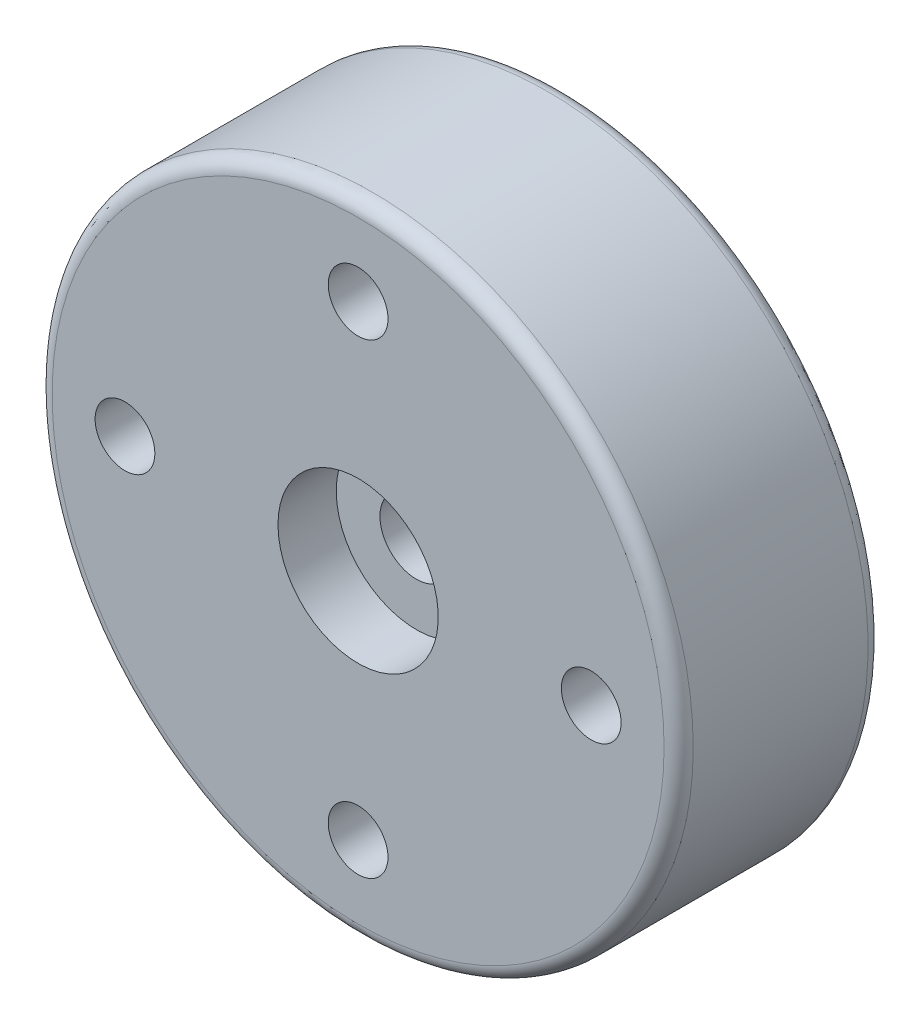
SolidWorks part; units mm, degrees
ref_plane "Front" through (0, 0, 0) normal (0, 0, 1) x (1, 0, 0)
ref_plane "Top" through (0, 0, 0) normal (0, 1, 0) x (1, 0, 0)
ref_plane "Right" through (0, 0, 0) normal (1, 0, 0) x (0, 0, -1)
sketch "Sketch1" plane through (0, 0, 0) normal (1, 0, 0) x (0, 0, -1)
  line L0 (0, 0) -> (-91.1734, 0) construction
  line L1 (3.5, 1.25) -> (2, 1.25)
  line L2 (0, 2.75) -> (0, 11)
  line L3 (0, 11) -> (7, 11)
  line L4 (7, 11) -> (7, 2.75)
  line L5 (7, 2.75) -> (3.5, 2.75)
  line L8 (3.5, 2.75) -> (3.5, 1.25)
  line L9 (0, 2.75) -> (2, 2.75)
  line L10 (2, 2.75) -> (2, 1.25)
  dimension "D1" = 2.5
  dimension "D2" = 5.5
  dimension "D3" = 2
  dimension "D4" = 7
  dimension "D5" = 22
  dimension "D6" = 1.5
revolve "Revolve1" add sketch "Sketch1" angle 360 about L0
hole_wizard "M2 Tapped Hole1" positions "Sketch3" profile "Sketch4" tap size "M2" standard "ISO" end condition up to next
sketch "Sketch3" plane through (0, 0, 0) normal (0, 0, 1) x (1, 0, 0)
  circle A0 centre (0, 0) radius 8 construction
  point P0 (0, 8)
  point P14 (8, 0)
  point P15 (0, -8)
  point P16 (-8, 0)
  point P17 (0, 0)
  dimension "D1" = 16
  dimension "D2" = 4
sketch "Sketch4" plane through (0, 8, 0) normal (1, 0, 0) x (0, -1, 0)
  line L0 (0, 0) -> (0, 7)
  line L1 (0, 7) -> (1.025, 7)
  line L2 (0.8, 6.8701) -> (0.8, 0.1299)
  line L3 (0.8, 0.1299) -> (1.025, 0)
  line L5 (1.025, 0) -> (0, 0)
  line L6 (-0.8, 0.1299) -> (-1.025, 0) construction
  line L7 (1.025, 7) -> (0.8, 6.8701)
  line L8 (-1.025, 7) -> (-0.8, 6.8701) construction
  line L11 (0, -6.35) -> (0, 107.95) construction
  dimension "Thru Tap Drill Dia." = 1.6
  dimension "Thru Tap Drill Depth" = 7
  dimension "Near C'Sink Dia." = 2.05
  dimension "Near C'Sink Angle" = 120
  dimension "Far C'Sink Dia." = 2.05
  dimension "Far C'Sink Angle" = 120
cosmetic thread "Hole Thread1" parameters "D2"=2
cosmetic thread "Hole Thread2" parameters "D2"=2
cosmetic thread "Hole Thread3" parameters "D2"=2
cosmetic thread "Hole Thread4" parameters "D2"=2
fillet "Radyus1" radius 0.5 2 edges at (-11, 0, -7) (-11, 0, 0)
sketch "Çizim1" plane through (0, 0, 0) normal (0, 0, 1) x (1, 0, 0)
  circle A0 centre (0, 8) radius 1.025
  circle A1 centre (-8, 0) radius 1.025
  circle A2 centre (8, 0) radius 1.025
  circle A3 centre (0, -8) radius 1.025
extrude "Kes-Ekstrüzyon1" cut sketch "Çizim1" against normal blind 10
